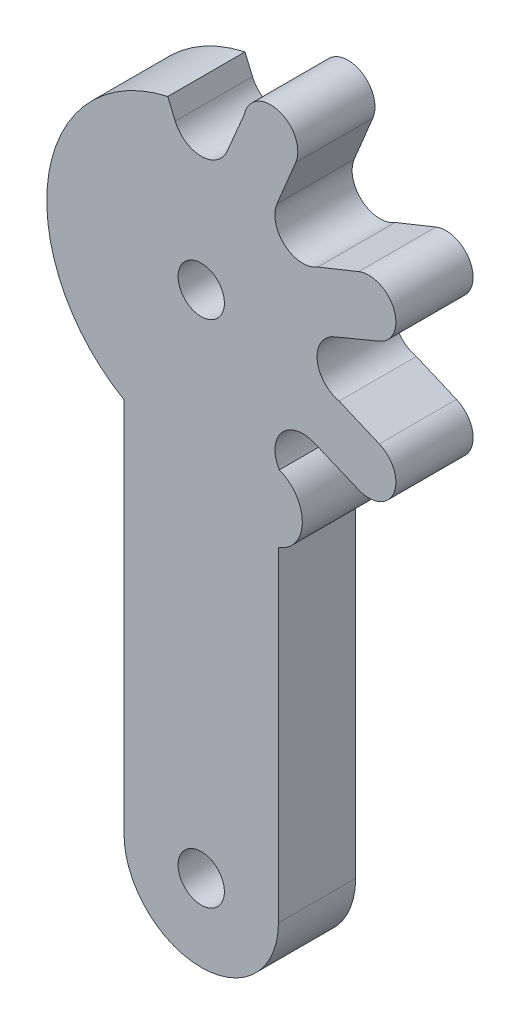
SolidWorks part; units mm, degrees
material "Acrylic (Medium-high impact)"
ref_plane "Front Plane" through (0, 0, 0) normal (0, 0, 1) x (1, 0, 0)
ref_plane "Top Plane" through (0, 0, 0) normal (0, 1, 0) x (1, 0, 0)
ref_plane "Right Plane" through (0, 0, 0) normal (1, 0, 0) x (0, 0, -1)
sketch "Sketch2" plane through (0, 0, 0) normal (0, 0, 1) x (1, 0, 0)
  line L0 (0, 0) -> (0, -33) construction
  line L3 (0, 0) -> (0, 27.439) construction
  line L17 (2.7867, 11.2193) -> (1.6793, 8.6201)
  line L18 (6.1108, 10.1869) -> (4.9079, 7.2828)
  line L22 (10.1845, 6.1157) -> (7.5635, 5.0609)
  line L25 (4.9998, -11.9435) -> (5, -33)
  line L26 (-5, -8.6603) -> (-5, -33)
  line L27 (11.5242, 2.8823) -> (8.6201, 1.6793)
  line L30 (11.5259, -2.8771) -> (8.9268, -1.7697)
  line L31 (10.1869, -6.1108) -> (7.2828, -4.9079)
  line L52 (-2.1661, 9.7626) -> (-1.6793, 8.6201)
  arc A1 (-5, -33) -> (5, -33) centre (0, -33) ccw
  circle A3 centre (0, -33) radius 1.5
  circle A4 centre (0, 0) radius 13.5 construction
  circle A5 centre (0, 0) radius 7.5 construction
  circle A24 centre (0, 0) radius 1.5
  arc A30 (2.7867, 11.2193) -> (6.1108, 10.1869) centre (4.5032, 10.8785) cw
  arc A32 (10.1845, 6.1157) -> (11.5242, 2.8823) centre (10.8545, 4.499) cw
  arc A37 (11.5259, -2.8771) -> (10.1869, -6.1108) centre (10.8564, -4.4939) cw
  arc A46 (-5, -8.6603) -> (-2.1661, 9.7626) centre (0, 0) cw
  arc A53 (7.5635, 5.0609) -> (4.9079, 7.2828) centre (6.5843, 6.5884) cw
  arc A55 (8.9268, -1.7697) -> (8.6201, 1.6793) centre (9.3145, 0.0029) cw
  arc A57 (5.0607, -7.5635) -> (7.2828, -4.9079) centre (6.5882, -6.5842) cw
  arc A67 (1.6793, 8.6201) -> (-1.6793, 8.6201) centre (0, 9.3074) cw
  arc A68 (4.9998, -11.9435) -> (5.0607, -7.5635) centre (4.207, -9.7421) ccw
  point P3 (0, -16.5)
  dimension "D1" = 5
  dimension "D8" = 3
  dimension "D9" = 27
  dimension "D10" = 15
  dimension "D11" = 3.9551
  dimension "D12" = 10
  dimension "D13" = 1.2418
  dimension "D14" = 1.8339
  dimension "D15" = 1.8145
  dimension "D16" = 2.8252
  dimension "D17" = 1.8339
  dimension "D18" = 1.1425
  dimension "D29" = 2.6209
  dimension "D7" = 4.4969
  dimension "D22" = 3
  dimension "D35" = 2.8252
  dimension "D19" = 1.75
  dimension "D24" = 1.8145
  dimension "D27" = 2.0894
  dimension "D33" = 1.8145
  dimension "D37" = 1.75
  dimension "D41" = 1.8145
  dimension "D43" = 2.3399
  dimension "D3" = 4.5032
  dimension "D4" = 33
  dimension "D5" = 4.2703
  dimension "D6" = 4.4961
  dimension "D20" = 2.9041
  dimension "D21" = 1.7473
  dimension "D23" = 3.1434
  dimension "D25" = 2.8252
  dimension "D26" = 1.871
  dimension "D28" = 4.499
  dimension "D30" = 2.9041
  dimension "D31" = 1.7473
  dimension "D32" = 1.2029
  dimension "D34" = 2.5992
  dimension "D36" = 1.871
  dimension "D38" = 2.9041
  dimension "D39" = 3.1434
  dimension "D40" = 1.7473
  dimension "D42" = 9.3143
  dimension "D44" = 10.6116
  dimension "D45" = 21.0565
  dimension "D46" = 24.3397
  dimension "D47" = 4.9997
  dimension "D48" = 5
extrude "Boss-Extrude1" add sketch "Sketch2" along normal blind 5
